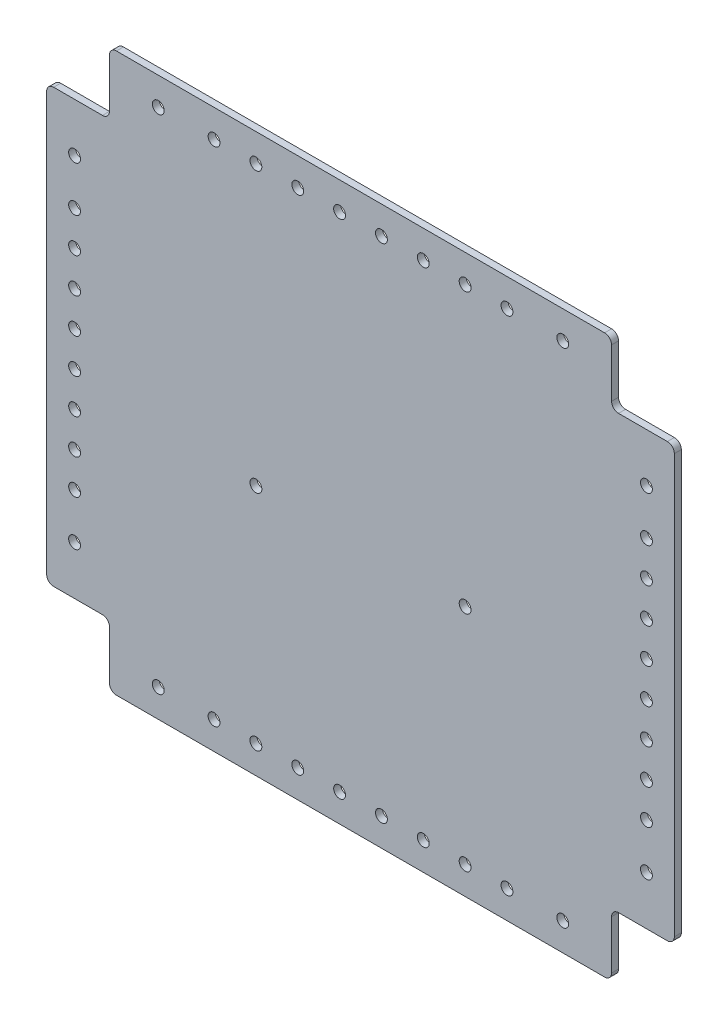
SolidWorks part; units mm, degrees
material "6061-T6 (SS)"
ref_plane "前视基准面" through (0, 0, 0) normal (0, 0, 1) x (1, 0, 0)
ref_plane "上视基准面" through (0, 0, 0) normal (0, 1, 0) x (1, 0, 0)
ref_plane "右视基准面" through (0, 0, 0) normal (1, 0, 0) x (0, 0, -1)
sketch "草图1" plane through (0, 0, 0) normal (0, 0, 1) x (1, 0, 0)
  line L1 (225, -200) -> (-225, -200)
  line L2 (225, -200) -> (225, 200)
  line L3 (225, 200) -> (-225, 200)
  line L4 (-225, -200) -> (-225, 200)
  line L5 (225, -200) -> (-225, 200) construction
  line L6 (225, 200) -> (-225, -200) construction
  line L7 (115, -100) -> (-115, -100) construction
  line L8 (115, -100) -> (115, 100) construction
  line L9 (115, 100) -> (-115, 100) construction
  line L10 (-115, -100) -> (-115, 100) construction
  line L11 (115, -100) -> (-115, 100) construction
  line L12 (115, 100) -> (-115, -100) construction
  circle A0 centre (-115, 100) radius 3.25 construction
  circle A1 centre (115, 100) radius 3.25 construction
  circle A2 centre (115, -100) radius 3.25 construction
  circle A3 centre (-115, -100) radius 3.25 construction
  point P0 (0, 0)
  point P6 (0, 0)
  dimension "D5" = 6.5
  dimension "D6" = 6.5
  dimension "D7" = 6.5
  dimension "D8" = 6.5
  dimension "D1" = 450
  dimension "D2" = 400
  dimension "D3" = 200
  dimension "D4" = 230
extrude "凸台-拉伸1" add sketch "草图1" along normal blind 5
sketch "草图3" plane through (0, 0, 5) normal (0, 0, 1) x (1, 0, 0)
  line L0 (225, -200) -> (225, 200) construction
  line L1 (-225, -200) -> (225, -200) construction
  line L2 (205, -180) -> (205, -120) construction
  line L3 (145, -180) -> (205, -180) construction
  line L4 (0, 200) -> (0, 0) construction
  line L5 (225, 200) -> (-225, 200) construction
  line L6 (0, 0) -> (-225, 0) construction
  line L7 (-225, 200) -> (-225, -200) construction
  line L8 (145, 180) -> (205, 180) construction
  line L9 (205, 180) -> (205, 120) construction
  line L10 (-205, 180) -> (-205, 120) construction
  line L11 (-145, 180) -> (-205, 180) construction
  line L12 (-145, -180) -> (-205, -180) construction
  line L13 (-205, -180) -> (-205, -120) construction
  circle A0 centre (205, -180) radius 3.75
  circle A1 centre (205, -120) radius 4.25
  circle A2 centre (145, -180) radius 4.25
  circle A3 centre (145, 180) radius 4.25
  circle A4 centre (205, 120) radius 4.25
  circle A5 centre (205, 180) radius 3.75
  circle A6 centre (-205, 180) radius 3.75
  circle A7 centre (-205, 120) radius 4.25
  circle A8 centre (-145, 180) radius 4.25
  circle A9 centre (-145, -180) radius 4.25
  circle A10 centre (-205, -120) radius 4.25
  circle A11 centre (-205, -180) radius 3.75
  dimension "D1" = 7.5
  dimension "D2" = 20
  dimension "D3" = 20
  dimension "D4" = 8.5
  dimension "D5" = 60
  dimension "D6" = 8.5
  dimension "D7" = 60
extrude "切除-拉伸2" cut sketch "草图3" against normal blind 50
sketch "草图4" plane through (0, 0, 5) normal (0, 0, 1) x (1, 0, 0)
  line L0 (225, 0) -> (0, 0) construction
  line L1 (225, -200) -> (225, 200) construction
  line L2 (0, -200) -> (0, 200) construction
  line L3 (225, 200) -> (-225, 200) construction
  line L4 (100, 0) -> (-100, 0) construction
  line L5 (100, -12.5) -> (-100, -12.5)
  line L6 (100, 12.5) -> (-100, 12.5)
  line L7 (100, 60) -> (-100, 60) construction
  line L8 (100, 47.5) -> (-100, 47.5)
  line L9 (100, 72.5) -> (-100, 72.5)
  line L10 (100, -60) -> (-100, -60) construction
  line L11 (100, -47.5) -> (-100, -47.5)
  line L12 (100, -72.5) -> (-100, -72.5)
  line L13 (100, 140) -> (-100, 140) construction
  line L14 (100, 127.5) -> (-100, 127.5)
  line L15 (100, 152.5) -> (-100, 152.5)
  line L16 (100, -140) -> (-100, -140) construction
  line L17 (100, -127.5) -> (-100, -127.5)
  line L18 (100, -152.5) -> (-100, -152.5)
  arc A0 (100, -12.5) -> (100, 12.5) centre (100, 0) ccw
  arc A1 (-100, 12.5) -> (-100, -12.5) centre (-100, 0) ccw
  arc A2 (100, 47.5) -> (100, 72.5) centre (100, 60) ccw
  arc A3 (-100, 72.5) -> (-100, 47.5) centre (-100, 60) ccw
  arc A4 (100, -47.5) -> (100, -72.5) centre (100, -60) cw
  arc A5 (-100, -72.5) -> (-100, -47.5) centre (-100, -60) cw
  arc A6 (100, 127.5) -> (100, 152.5) centre (100, 140) ccw
  arc A7 (-100, 152.5) -> (-100, 127.5) centre (-100, 140) ccw
  arc A8 (100, -127.5) -> (100, -152.5) centre (100, -140) cw
  arc A9 (-100, -152.5) -> (-100, -127.5) centre (-100, -140) cw
  point P10 (0, 0)
  point P19 (0, 60)
  point P25 (0, -60)
  point P32 (0, 140)
  point P39 (0, -140)
  dimension "D2" = 200
  dimension "D1" = 25
  dimension "D4" = 60
  dimension "D6" = 80
  dimension "D3" = 2
  dimension "D5" = 2
extrude "切除-拉伸3" [suppressed] cut sketch "草图4" against normal blind 50
sketch "草图5" plane through (0, 0, 5) normal (0, 0, 1) x (1, 0, 0)
  line L0 (0, 0) -> (253.0998, 0) construction
  line L1 (225, -200) -> (180, -200)
  line L2 (225, -200) -> (225, -155)
  line L3 (225, -155) -> (180, -155)
  line L4 (180, -200) -> (180, -155)
  line L5 (202.5, -155) -> (202.5, -200) construction
  line L6 (225, -177.5) -> (180, -177.5) construction
  line L7 (0, 0) -> (0, 234.088) construction
  line L8 (-225, -177.5) -> (-180, -177.5) construction
  line L9 (-202.5, -155) -> (-202.5, -200) construction
  line L10 (-180, -200) -> (-180, -155)
  line L11 (-225, -155) -> (-180, -155)
  line L12 (-225, -200) -> (-225, -155)
  line L13 (-225, -200) -> (-180, -200)
  line L14 (-202.5, 155) -> (-202.5, 200) construction
  line L15 (-225, 177.5) -> (-180, 177.5) construction
  line L16 (225, 177.5) -> (180, 177.5) construction
  line L17 (202.5, 155) -> (202.5, 200) construction
  line L18 (-225, 200) -> (-180, 200)
  line L19 (-225, 200) -> (-225, 155)
  line L20 (-225, 155) -> (-180, 155)
  line L21 (-180, 200) -> (-180, 155)
  line L22 (180, 200) -> (180, 155)
  line L23 (225, 155) -> (180, 155)
  line L24 (225, 200) -> (225, 155)
  line L25 (225, 200) -> (180, 200)
  point P15 (-202.5, -177.5)
  point P32 (202.5, 177.5)
  point P33 (-202.5, 177.5)
  point P52 (202.5, -177.5)
  dimension "D1" = 45
  dimension "D2" = 45
extrude "切除-拉伸4" cut sketch "草图5" against normal blind 56
fillet "圆角1" radius 5 12 edges at (180, 200, 2.5) (-180, 155, 2.5) (-225, -155, 2.5) (-180, -155, 2.5) (-180, -200, 2.5) (180, -200, 2.5) (180, -155, 2.5) (225, -155, 2.5) (225, 155, 2.5) (180, 155, 2.5) (-225, 155, 2.5) (-180, 200, 2.5)
sketch "草图6" plane through (0, 0, 0) normal (0, 0, -1) x (-1, 0, 0)
  line L0 (0, 0) -> (0, -200) construction
  line L1 (175, -200) -> (-175, -200) construction
  line L2 (75, -180) -> (-145, -180) construction
  circle A0 centre (75, -180) radius 4.25
  circle A1 centre (-75, -180) radius 4.25
  circle A2 centre (-75, -20) radius 4.25
  circle A3 centre (75, -20) radius 4.25
  dimension "D1" = 8.5
  dimension "D4" = 160
  dimension "D2" = 150
  dimension "D3" = 2
extrude "切除-拉伸5" cut sketch "草图6" against normal blind 90
sketch "草图7" plane through (0, 0, 0) normal (0, 0, -1) x (-1, 0, 0)
  line L0 (0, 200) -> (0, 0) construction
  line L1 (-175, 200) -> (175, 200) construction
  line L2 (0, 0) -> (-225, 0) construction
  line L3 (-225, -150) -> (-225, 150) construction
  line L4 (-205, -120) -> (-205, 120) construction
  line L5 (-145, 180) -> (145, 180) construction
  circle A0 centre (-15, 180) radius 4.25
  circle A1 centre (-45, 180) radius 4.25
  circle A2 centre (-75, 180) radius 4.25
  circle A3 centre (-105, 180) radius 4.25
  circle A4 centre (-205, 12.5) radius 4.25
  circle A5 centre (-205, 37.5) radius 4.25
  circle A6 centre (-205, 62.5) radius 4.25
  circle A7 centre (-205, 87.5) radius 4.25
  circle A8 centre (-205, -87.5) radius 4.25
  circle A9 centre (-205, -62.5) radius 4.25
  circle A10 centre (-205, -37.5) radius 4.25
  circle A11 centre (-205, -12.5) radius 4.25
  circle A12 centre (205, -12.5) radius 4.25
  circle A13 centre (205, -37.5) radius 4.25
  circle A14 centre (205, -62.5) radius 4.25
  circle A15 centre (205, -87.5) radius 4.25
  circle A16 centre (205, 87.5) radius 4.25
  circle A17 centre (205, 62.5) radius 4.25
  circle A18 centre (205, 37.5) radius 4.25
  circle A19 centre (205, 12.5) radius 4.25
  circle A20 centre (105, 180) radius 4.25
  circle A21 centre (75, 180) radius 4.25
  circle A22 centre (45, 180) radius 4.25
  circle A23 centre (15, 180) radius 4.25
  circle A24 centre (15, -180) radius 4.25
  circle A25 centre (45, -180) radius 4.25
  circle A26 centre (75, -180) radius 4.25
  circle A27 centre (105, -180) radius 4.25
  circle A28 centre (-105, -180) radius 4.25
  circle A29 centre (-75, -180) radius 4.25
  circle A30 centre (-45, -180) radius 4.25
  circle A31 centre (-15, -180) radius 4.25
  dimension "D1" = 8.5
  dimension "D2" = 30
  dimension "D4" = 30
  dimension "D5" = 8.5
  dimension "D6" = 25
  dimension "D8" = 25
  dimension "D3" = 4
  dimension "D7" = 4
extrude "切除-拉伸6" cut sketch "草图7" against normal blind 90
